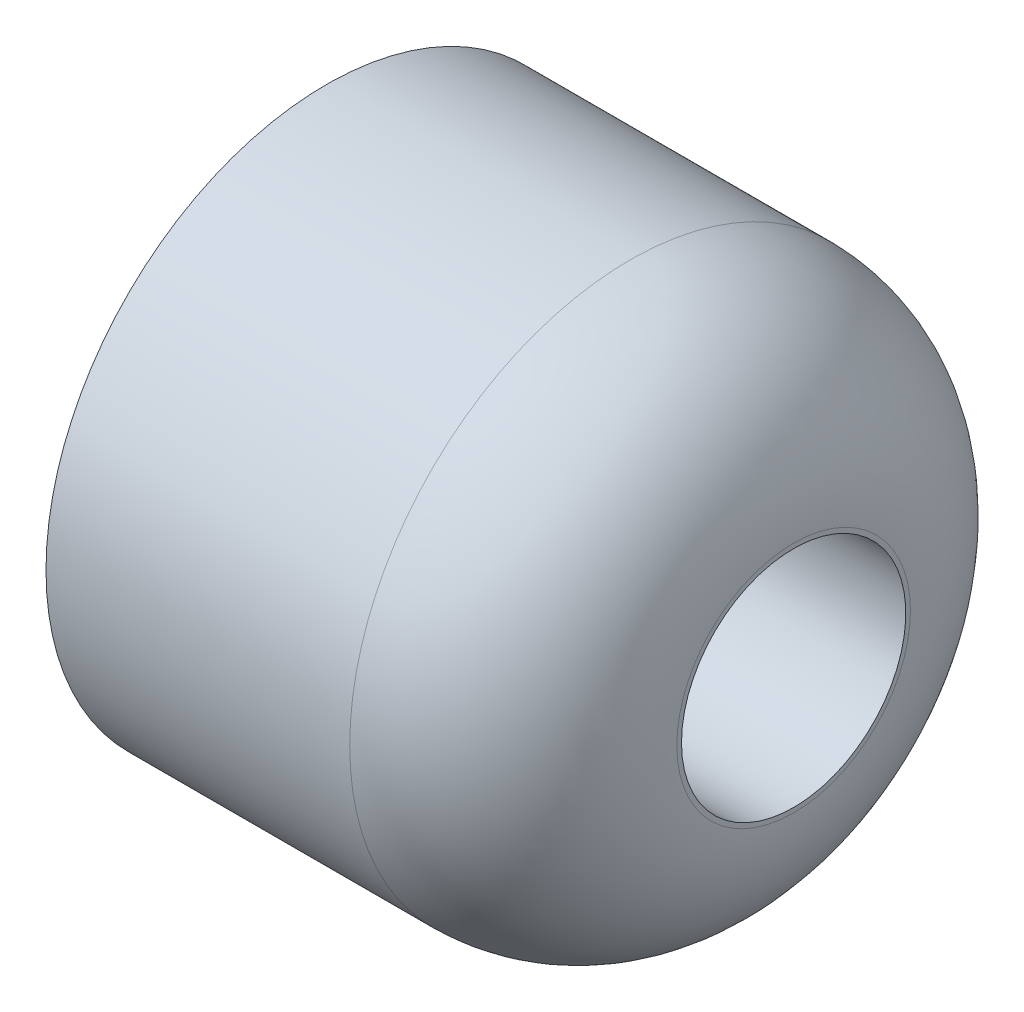
SolidWorks part; units mm, degrees
ref_plane "Front Plane" through (0, 0, 0) normal (1, 0, 0) x (0, 1, 0)
ref_plane "Top Plane" through (0, 0, 0) normal (0, 0, 1) x (0, 1, 0)
ref_plane "Right Plane" through (0, 0, 0) normal (0, 1, 0) x (-1, 0, 0)
sketch "Sketch1" plane through (0, 0, 0) normal (0, 1, 0) x (-1, 0, 0)
  line L7 (0, 0) -> (-18.7537, 0) construction
  line L8 (-10, 2.4) -> (0, 2.4)
  line L9 (0, 2.4) -> (0, 3.9)
  line L10 (0, 3.9) -> (-6, 3.9)
  line L11 (-6, 3.9) -> (-6, 5.5)
  line L12 (-6, 5.5) -> (0, 5.5)
  line L13 (0, 5.5) -> (0, 6)
  line L14 (-10, 2.4) -> (-10, 2.5)
  line L15 (-6.5, 6) -> (0, 6)
  arc A0 (-6.5, 6) -> (-10, 2.5) centre (-6.5, 2.5) ccw
  dimension "D7" = 3.5
  dimension "D1" = 10
  dimension "D2" = 6
  dimension "D3" = 6
  dimension "D4" = 2.4
  dimension "D5" = 3.9
  dimension "D6" = 5.5
revolve "Revolve1" add sketch "Sketch1" angle 360 about L7
